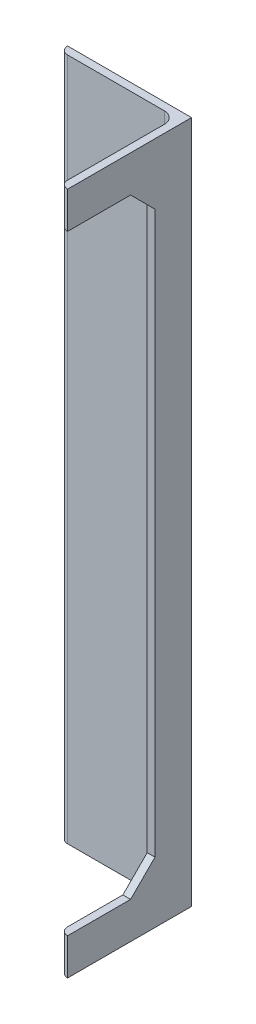
SolidWorks part; units mm, degrees
ref_plane "Alzado" through (0, 0, 0) normal (0, 0, 1) x (1, 0, 0)
ref_plane "Planta" through (0, 0, 0) normal (0, 1, 0) x (1, 0, 0)
ref_plane "Vista lateral" through (0, 0, 0) normal (1, 0, 0) x (0, 0, -1)
sketch "Croquis1" plane through (0, 0, 0) normal (0, 0, 1) x (1, 0, 0)
  line L0 (0, 0) -> (0, 280)
  dimension "D1" = 280
sketch "Croquis13" plane through (0, 0, 0) normal (0, 1, 0) x (1, 0, 0)
  line L0 (0, 0) -> (38, 0)
  line L1 (0, 0) -> (0, 38)
  line L2 (3, 3) -> (3, 38)
  line L3 (3, 3) -> (38, 3)
  line L4 (38, 0) -> (38, 3)
  line L5 (3, 38) -> (0, 38)
  dimension "D1" = 38
  dimension "D2" = 3
other "Angular ALUMINIO ANGULAR 38MM(1)"
ref_plane "Plano1" through (0, 0, 0) normal (0, 1, 0) x (-1, 0, 0)
sketch "Sketch11" plane through (0, 0, 0) normal (0, 1, 0) x (-1, 0, 0)
  line L0 (0, 0) -> (0, 50.8)
  line L1 (0, 50.8) -> (0.0051, 50.8)
  line L2 (3.175, 47.6301) -> (3.175, 7.9375)
  line L3 (7.9375, 3.175) -> (47.6301, 3.175)
  line L4 (50.8, 0.0051) -> (50.8, 0)
  line L5 (50.8, 0) -> (0, 0)
  arc A0 (50.8, 0.0051) -> (47.6301, 3.175) centre (47.6301, 0.0051) ccw
  arc A1 (0.0051, 50.8) -> (3.175, 47.6301) centre (0.0051, 47.6301) cw
  arc A2 (7.9375, 3.175) -> (3.175, 7.9375) centre (7.9375, 7.9375) cw
  point P10 (25.4, 0)
  point P14 (0, 25.4)
  point P15 (3.175, 25.4)
  point P16 (25.4, 3.175)
  point P17 (3.175, 50.8)
  point P18 (50.8, 3.175)
  point P19 (0, 0)
  dimension "D2" = 0.0051
  dimension "Radius_1" = 4.7625
  dimension "D1" = 3.175
  dimension "H_leg" = 50.8
sketch "Croquis8" plane through (0, 0, 0) normal (1, 0, 0) x (0, 0, -1)
  line L0 (-15, 0) -> (-15, 280) construction
  line L1 (-50.8, 0) -> (0, 0) construction
  line L2 (-50.8, 280) -> (0, 280) construction
  line L3 (-50.8, 140) -> (0, 140) construction
  line L4 (-50.8, 280) -> (-50.8, 0) construction
  line L5 (0, 280) -> (0, 0) construction
  line L6 (-50.8, 15) -> (0, 15) construction
  line L7 (-50.8, 15) -> (-15, 15)
  line L8 (-15, 15) -> (-15, 265)
  line L9 (-50.8, 265) -> (-15, 265)
  line L10 (-50.8, 15) -> (-50.8, 265)
  point P17 (-15, 140)
  dimension "D1" = 15
  dimension "D2" = 15
extrude "Cortar-Extruir1" cut sketch "Croquis8" against normal blind 4
chamfer "Chaflán1" distance 10 angle 45 2 edges at (-1.5875, 265, 15) (-1.5875, 15, 15)
sketch "Croquis9" plane through (0, 0, 0) normal (0, 0, -1) x (-1, 0, 0)
  line L0 (50.8, 280) -> (50.8, 0) construction
  line L1 (50.8, 280) -> (50.8, 0)
  line L4 (32, 280) -> (50.8, 280)
  line L5 (32, 280) -> (32, 0)
  line L6 (32, 280) -> (32, 0)
  line L7 (32, 0) -> (50.8, 0)
  dimension "D1" = 32
sketch "Croquis10" plane through (0, 0, 0) normal (0, 0, -1) x (-1, 0, 0)
  circle A0 centre (5.675, 41) radius 2 construction
  circle A1 centre (5.675, 41) radius 2
  circle A2 centre (5.675, 11) radius 2 construction
  circle A3 centre (5.675, 11) radius 2
  circle A4 centre (-44.325, 41) radius 2 construction
  circle A5 centre (-44.325, 41) radius 2
  circle A6 centre (-44.325, 11) radius 2 construction
  circle A7 centre (-44.325, 11) radius 2
extrude "Cortar-Extruir3" cut sketch "Croquis10" against normal blind 10
sketch "Croquis12" plane through (0, 0, 0) normal (0, 0, -1) x (-1, 0, 0)
  circle A0 centre (5.675, 269) radius 2 construction
  circle A1 centre (5.675, 239) radius 2 construction
  circle A2 centre (5.675, 269) radius 2
  circle A3 centre (5.675, 239) radius 2
extrude "Cortar-Extruir4" cut sketch "Croquis12" against normal blind 10
